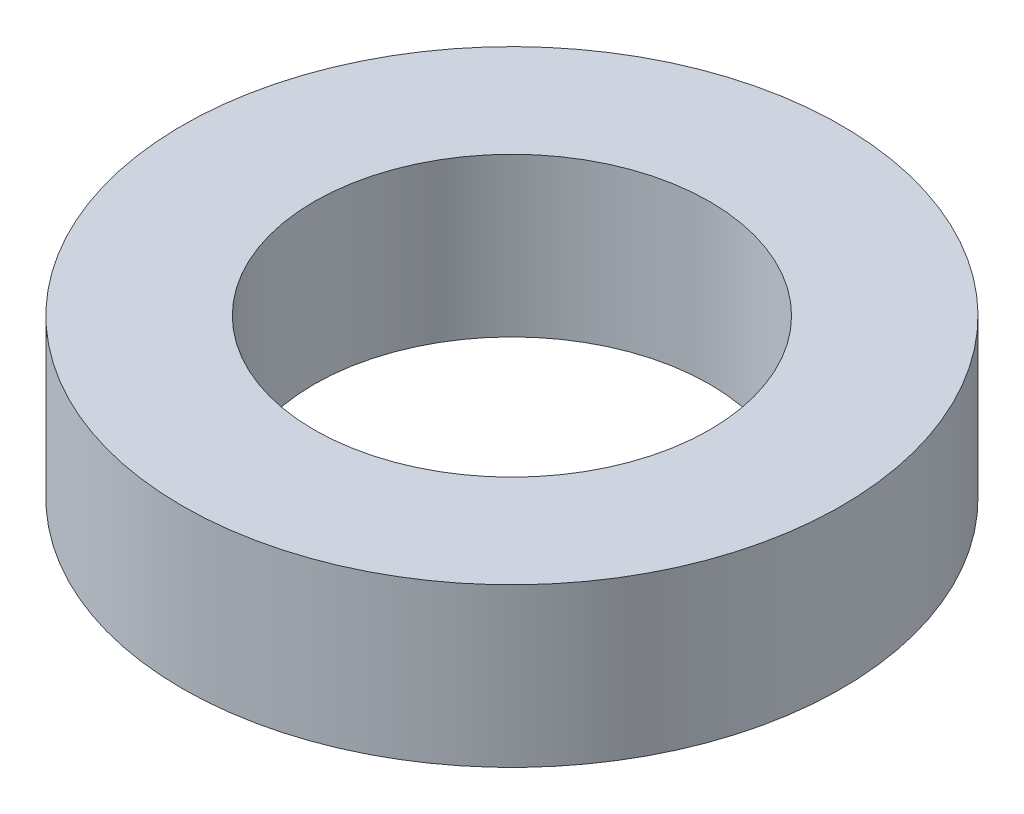
SolidWorks part; units mm, degrees
ref_plane "Front Plane" through (0, 0, 0) normal (0, 0, 1) x (1, 0, 0)
ref_plane "Top Plane" through (0, 0, 0) normal (0, 1, 0) x (1, 0, 0)
ref_plane "Right Plane" through (0, 0, 0) normal (1, 0, 0) x (0, 0, -1)
sketch "Sketch1" plane through (0, 0, 0) normal (0, 1, 0) x (1, 0, 0)
  circle A0 centre (0, 0) radius 4.7625
  circle A1 centre (0, 0) radius 7.9375
  dimension "D1" = 3.175
  dimension "D2" = 9.525
extrude "Boss-Extrude1" add sketch "Sketch1" along normal blind 3.81
